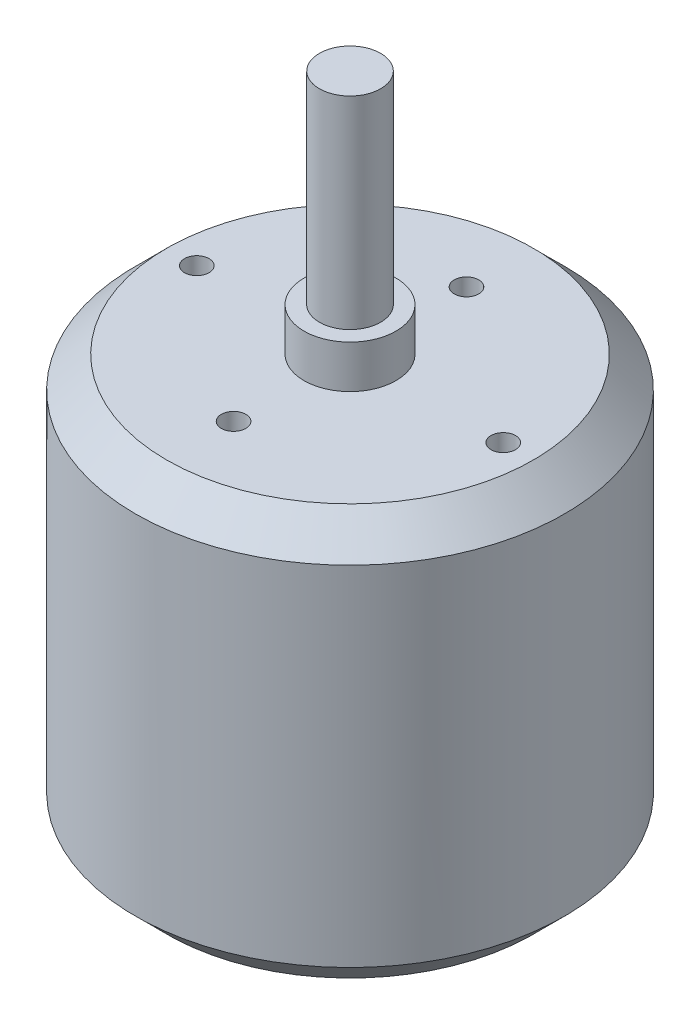
SolidWorks part; units mm, degrees
ref_plane "Front Plane" through (0, 0, 0) normal (0, 0, 1) x (1, 0, 0)
ref_plane "Top Plane" through (0, 0, 0) normal (0, 1, 0) x (1, 0, 0)
ref_plane "Right Plane" through (0, 0, 0) normal (1, 0, 0) x (0, 0, -1)
sketch "Sketch1" plane through (0, 0, 0) normal (0, 1, 0) x (1, 0, 0)
  circle A0 centre (0, 0) radius 17.5
  dimension "D1" = 35
extrude "Boss-Extrude1" add sketch "Sketch1" along normal blind 24
sketch "Sketch2" plane through (0, 24, 0) normal (0, 1, 0) x (1, 0, 0)
  circle A0 centre (0, 0) radius 3.75
  dimension "D1" = 7.5
extrude "Boss-Extrude2" add sketch "Sketch2" along normal blind 3.5
sketch "Sketch3" plane through (0, 27.5, 0) normal (0, 1, 0) x (1, 0, 0)
  circle A0 centre (0, 0) radius 2.5
  dimension "D1" = 5
extrude "Boss-Extrude3" add sketch "Sketch3" along normal blind 16.5
chamfer "Chamfer1" distance 2.54 angle 45 1 edges at (0, 24, 17.5)
sketch "Sketch5" plane through (0, 0, 0) normal (0, -1, 0) x (1, 0, 0)
  circle A1 centre (0, 0) radius 17.5
  circle A2 centre (0, 0) radius 17.5
  dimension "D1" = 0
extrude "Boss-Extrude4" add sketch "Sketch5" along normal blind 9.5
chamfer "Chamfer2" distance 2.54 angle 45 1 edges at (0, -9.5, -17.5)
sketch "Sketch6" plane through (0, -9.5, 0) normal (0, -1, 0) x (1, 0, 0)
  circle A0 centre (0, 0) radius 3
  dimension "D1" = 6
extrude "Boss-Extrude5" add sketch "Sketch6" along normal blind 1
sketch "Sketch7" plane through (0, 24, 0) normal (0, 1, 0) x (1, 0, 0)
  line L0 (0, 0) -> (12.5, 0) construction
  line L1 (0, 0) -> (0, 9.5) construction
  circle A0 centre (0, 9.5) radius 1
  circle A1 centre (12.5, 0) radius 1
  circle A2 centre (0, -9.5) radius 1
  circle A3 centre (-12.5, 0) radius 1
  point P5 (9.4026, 0)
  dimension "D1" = 2
  dimension "D2" = 9.5
  dimension "D3" = 12.5
extrude "Cut-Extrude1" cut sketch "Sketch7" against normal blind 25.4
